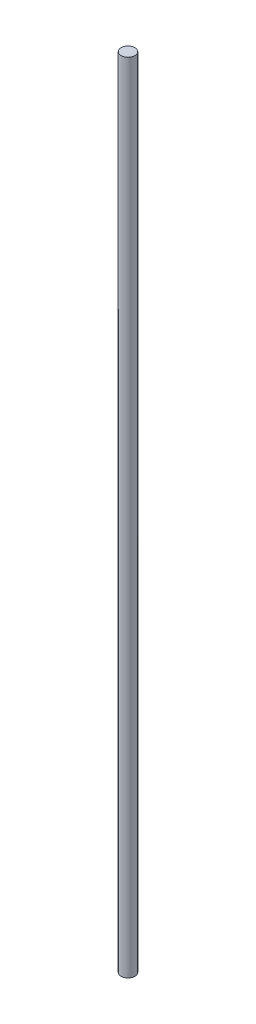
SolidWorks part; units mm, degrees
ref_plane "Front Plane" through (0, 0, 0) normal (0, 0, 1) x (1, 0, 0)
ref_plane "Top Plane" through (0, 0, 0) normal (0, 1, 0) x (1, 0, 0)
ref_plane "Right Plane" through (0, 0, 0) normal (1, 0, 0) x (0, 0, -1)
sketch "Sketch2" plane through (0, 0, 0) normal (0, 0, 1) x (1, 0, 0)
  line L0 (0, 0) -> (0, 304.1978) construction
  line L1 (0, 0) -> (-4.7625, 0)
  line L2 (0, 0) -> (0, 550)
  line L3 (-4.7625, 0) -> (-4.7625, 550)
  line L4 (0, 550) -> (-4.7625, 550)
  dimension "D1" = 550
  dimension "D2" = 4.7625
revolve "Revolve1" add sketch "Sketch2" angle 360 about L0
